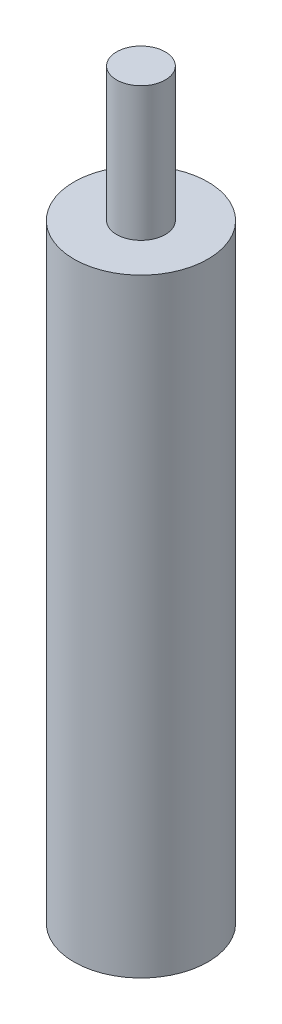
SolidWorks part; units mm, degrees
material "Alliage 1060"
ref_plane "Plan de face" through (0, 0, 0) normal (0, 0, 1) x (1, 0, 0)
ref_plane "Plan de dessus" through (0, 0, 0) normal (0, 1, 0) x (1, 0, 0)
ref_plane "Plan de droite" through (0, 0, 0) normal (1, 0, 0) x (0, 0, -1)
sketch "Esquisse1" plane through (0, 0, 0) normal (0, 1, 0) x (1, 0, 0)
  circle A0 centre (0, 0) radius 5.5
  dimension "D1" = 11
extrude "Boss.-Extru.1" add sketch "Esquisse1" along normal blind 50
sketch "Esquisse2" plane through (0, 50, 0) normal (0, 1, 0) x (1, 0, 0)
  circle A0 centre (0, 0) radius 2
  dimension "D1" = 4
extrude "Boss.-Extru.2" add sketch "Esquisse2" along normal blind 11
sketch "Esquisse3" plane through (0, 0, 0) normal (0, -1, 0) x (1, 0, 0)
  circle A0 centre (0, 0) radius 2
  dimension "D1" = 4
extrude "Enlèv. mat.-Extru.1" cut sketch "Esquisse3" against normal blind 11
